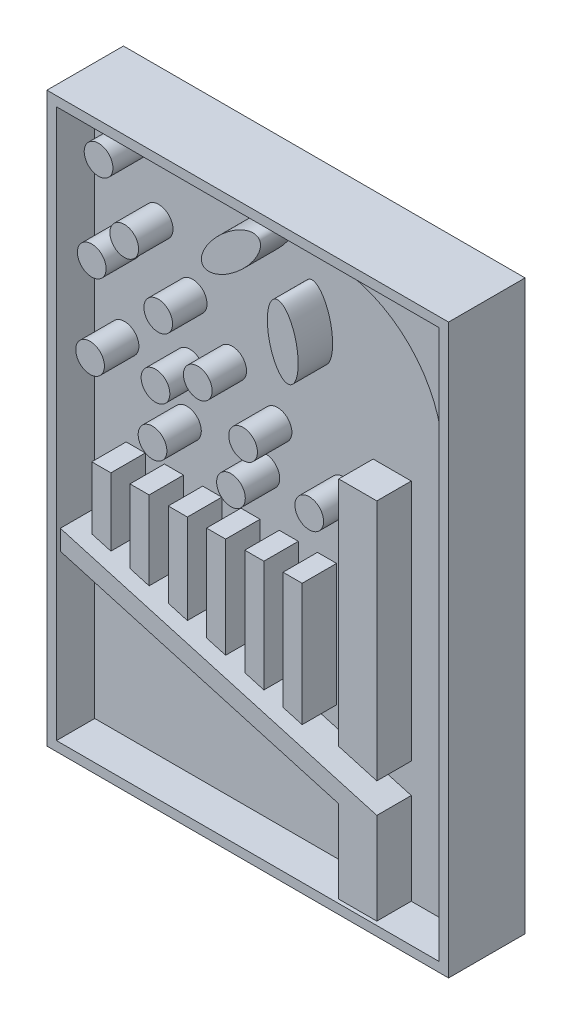
SolidWorks part; units mm, degrees
ref_plane "前基準面" through (0, 0, 0) normal (0, 0, 1) x (1, 0, 0)
ref_plane "上基準面" through (0, 0, 0) normal (0, 1, 0) x (1, 0, 0)
ref_plane "右基準面" through (0, 0, 0) normal (1, 0, 0) x (0, 0, -1)
sketch "草圖1" plane through (0, 0, 0) normal (0, 0, 1) x (1, 0, 0)
  line L1 (-105, 148.5) -> (105, 148.5)
  line L2 (-105, 148.5) -> (-105, -148.5)
  line L3 (-105, -148.5) -> (105, -148.5)
  line L4 (105, 148.5) -> (105, -148.5)
  line L5 (-105, 148.5) -> (105, -148.5) construction
  line L6 (-105, -148.5) -> (105, 148.5) construction
  point P0 (0, 0)
  dimension "D1" = 210
  dimension "D2" = 297
extrude "填料-伸長1" add sketch "草圖1" against normal blind 40
sketch "草圖2" plane through (0, 0, 0) normal (0, 0, 1) x (1, 0, 0)
  line L21 (100, -143.5) -> (100, 143.5)
  line L22 (100, 143.5) -> (-100, 143.5)
  line L23 (-100, 143.5) -> (-100, -143.5)
  line L24 (-100, -143.5) -> (100, -143.5)
  line L25 (100, -143.5) -> (100, 143.5)
  line L26 (100, 143.5) -> (-100, 143.5)
  line L27 (-100, 143.5) -> (-100, -143.5)
  line L28 (-100, -143.5) -> (100, -143.5)
  point P0 (0, 0)
  dimension "D1" = 5
extrude "除料-伸長1" cut sketch "草圖2" against normal blind 20
sketch "草圖3" plane through (0, 0, -20) normal (0, 0, 1) x (1, 0, 0)
  line L0 (65.4867, -143.5) -> (65.4867, -95.626)
  line L1 (-100, -143.5) -> (100, -143.5) construction
  line L2 (65.4867, 46.7716) -> (45.5652, 46.7716)
  line L3 (45.5652, 46.7716) -> (45.5652, -74.3368)
  line L4 (-100, -143.5) -> (100, -143.5) construction
  line L5 (65.4867, -95.626) -> (26.4395, -84.4744)
  line L6 (-100, 143.5) -> (-100, -143.5) construction
  line L7 (45.5652, -100.3364) -> (-100, -58.764)
  line L8 (42.819, -99.5521) -> (-102.7461, -57.9797) construction
  line L9 (45.5652, -89.9365) -> (-100, -48.3642) construction
  line L10 (26.4395, -74.0746) -> (16.4395, -71.2186)
  line L11 (65.4867, -80.0263) -> (45.5652, -74.3368)
  line L12 (69.6059, -81.2027) -> (-95.8808, -33.9409) construction
  line L13 (45.5652, -100.3364) -> (45.5652, -143.5)
  line L14 (65.4867, -80.0263) -> (65.4867, 46.7716)
  line L15 (45.5652, -143.5) -> (65.4867, -143.5)
  line L16 (-100, -48.3642) -> (-100, -58.764)
  line L17 (-83.5605, -10.0503) -> (-73.5605, -10.0503)
  line L18 (-83.5605, -10.0503) -> (-83.5605, -42.6594)
  line L19 (-63.5605, -10.0503) -> (-63.5605, -48.3712)
  line L20 (-73.5605, -10.0503) -> (-73.5605, -53.0592) construction
  line L21 (-53.5605, -10.0503) -> (-53.5605, -36.9951)
  line L22 (-73.5605, -10.0503) -> (-73.5605, -45.5153)
  line L23 (-33.5605, -10.0503) -> (-33.5605, -56.939)
  line L24 (-53.5605, -10.0503) -> (-53.5605, -51.2272)
  line L25 (-13.5605, -10.0503) -> (-13.5605, -62.6509)
  line L26 (-53.5605, -10.0503) -> (-53.5605, -53.0592) construction
  line L27 (-43.5605, -10.0503) -> (-43.5605, -54.0831)
  line L28 (-23.5605, -10.0503) -> (-23.5605, -59.7949)
  line L29 (-3.5605, -10.0503) -> (-3.5605, -65.5068)
  line L30 (6.4395, -10.0503) -> (6.4395, -68.3627)
  line L31 (-83.5605, -53.0592) -> (26.4395, -84.4744)
  line L32 (51.0574, -81.1053) -> (-94.5077, -39.5329) construction
  line L33 (-83.5605, -10.0503) -> (-83.5605, -53.0592) construction
  line L34 (-73.5605, -45.5153) -> (-83.5605, -42.6594)
  line L35 (16.4395, -10.0503) -> (16.4395, -71.2186)
  line L36 (26.4395, -10.0503) -> (26.4395, -74.0746)
  line L37 (-63.5605, -10.0503) -> (-53.5605, -10.0503)
  line L38 (-43.5605, -10.0503) -> (-33.5605, -10.0503)
  line L39 (-23.5605, -10.0503) -> (-13.5605, -10.0503)
  line L40 (-3.5605, -10.0503) -> (6.4395, -10.0503)
  line L41 (16.4395, -10.0503) -> (26.4395, -10.0503)
  line L42 (26.4395, -10.0503) -> (26.4395, -53.0592) construction
  line L43 (16.4395, -10.0503) -> (16.4395, -53.0592) construction
  line L44 (6.4395, -10.0503) -> (6.4395, -53.0592) construction
  line L45 (-3.5605, -10.0503) -> (-3.5605, -53.0592) construction
  line L46 (-13.5605, -10.0503) -> (-13.5605, -53.0592) construction
  line L47 (-23.5605, -10.0503) -> (-23.5605, -53.0592) construction
  line L48 (-33.5605, -10.0503) -> (-33.5605, -53.0592) construction
  line L49 (-43.5605, -10.0503) -> (-43.5605, -53.0592) construction
  line L50 (-53.5605, -10.0503) -> (-53.5605, -53.0592) construction
  line L51 (-63.5605, -10.0503) -> (-63.5605, -53.0592) construction
  line L52 (-53.5605, -51.2272) -> (-63.5605, -48.3712)
  line L53 (-83.5605, -53.0592) -> (-100, -48.3642)
  line L54 (65.4867, -95.626) -> (-100, -48.3642) construction
  line L55 (-33.5605, -56.939) -> (-43.5605, -54.0831)
  line L56 (-13.5605, -62.6509) -> (-23.5605, -59.7949)
  line L57 (6.4395, -68.3627) -> (-3.5605, -65.5068)
  line L58 (100, -143.5) -> (100, 143.5) construction
  line L61 (100, 143.5) -> (-100, 143.5) construction
  circle A0 centre (-80, 128.5) radius 7.5
  circle A1 centre (-66.5709, 98.5) radius 7.5
  circle A2 centre (-48.8048, 73.5) radius 7.5
  circle A4 centre (-28.1285, 53.5) radius 7.5
  circle A5 centre (30.154, 23.5) radius 7.5
  circle A6 centre (-4.4362, 37.5951) radius 7.5
  circle A7 centre (-83.5605, 81.097) radius 7.5
  circle A8 centre (-50.2398, 41.0804) radius 7.5
  circle A9 centre (-10.7827, 13.507) radius 7.5
  circle A10 centre (-84.4251, 36.5786) radius 7.5
  circle A11 centre (-51.7873, 14.4918) radius 7.5
  ellipse E0 centre (-10.7827, 121.2666) end of major axis (3.813, 134.6632) minor radius 7.5
  ellipse E1 centre (16.3068, 94.1771) end of major axis (13.0758, 111.8514) minor radius 7.5
  dimension "D19" = 30
  dimension "D16" = 30
  dimension "D22" = 15
  dimension "D23" = 15
  dimension "D24" = 15
  dimension "D25" = 15
  dimension "D26" = 15
  dimension "D27" = 15
  dimension "D31" = 15
  dimension "D32" = 15
  dimension "D33" = 15
  dimension "D34" = 15
  dimension "D35" = 15
  dimension "D17" = 25
  dimension "D18" = 20
  dimension "D20" = 20
  dimension "D21" = 15
  dimension "D28" = 15.9049
  dimension "D29" = 15
  dimension "D30" = 15
  dimension "D1" = 10
  dimension "D2" = 15
  dimension "D3" = 20
  dimension "D5" = 10
  dimension "D6" = 20
  dimension "D7" = 20
  dimension "D8" = 20
  dimension "D9" = 20
  dimension "D10" = 10
  dimension "D11" = 10
  dimension "D12" = 10
  dimension "D13" = 10
  dimension "D14" = 10
  dimension "D15" = 10
  dimension "D36" = 20
extrude "填料-伸長2" add sketch "草圖3" along normal blind 18
sketch "草圖4" plane through (0, 0, -20) normal (0, 0, 1) x (1, 0, 0)
  line L0 (100, 143.5) -> (-100, 143.5) construction
  line L1 (100, -143.5) -> (100, 143.5) construction
  line L2 (40, 143.5) -> (100, 143.5)
  line L3 (100, 143.5) -> (100, 83.5)
  arc A0 (40, 143.5) -> (100, 83.5) centre (40, 83.5) cw
  dimension "D3" = 60
  dimension "D1" = 60
  dimension "D2" = 60
extrude "填料-伸長3" add sketch "草圖4" along normal blind 18
